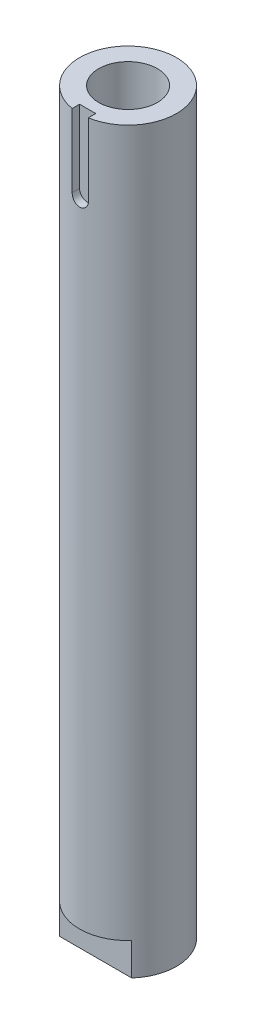
SolidWorks part; units mm, degrees
ref_plane "Front Plane" through (0, 0, 0) normal (0, 0, 1) x (1, 0, 0)
ref_plane "Top Plane" through (0, 0, 0) normal (0, 1, 0) x (1, 0, 0)
ref_plane "Right Plane" through (0, 0, 0) normal (1, 0, 0) x (0, 0, -1)
sketch "Sketch1" plane through (0, 0, 0) normal (0, 1, 0) x (1, 0, 0)
  circle A0 centre (0, 0) radius 9.5
  dimension "D1" = 19
extrude "Boss-Extrude1" add sketch "Sketch1" along normal blind 144.78
sketch "Sketch2" plane through (0, 0, 0) normal (0, -1, 0) x (-1, 0, 0)
  line L1 (7.0659, -6.35) -> (-7.0659, -6.35)
  line L3 (7.0659, 6.35) -> (-7.0659, 6.35)
  arc A2 (-7.0659, -6.35) -> (7.0659, -6.35) centre (0, 0) ccw
  arc A3 (7.0659, 6.35) -> (-7.0659, 6.35) centre (0, 0) ccw
  point P0 (0, 0)
  dimension "D1" = 12.7
  dimension "D2" = 6.35
extrude "Cut-Extrude1" cut sketch "Sketch2" against normal blind 6.35
hole_wizard "Tap Drill for 1/4-20 Tap1" positions "Sketch3" profile "Sketch4" hole size "1/4-20" standard "ANSI Inch"
sketch "Sketch3" plane through (0, 0, 0) normal (0, -1, 0) x (-1, 0, 0)
  point P0 (0, 0)
sketch "Sketch4" plane through (0, 0, 0) normal (1, 0, 0) x (0, 0, -1)
  line L0 (0, 0) -> (0, 33.2838)
  line L1 (0, 33.2838) -> (2.5527, 31.75)
  line L2 (2.5527, 31.75) -> (2.5527, 0)
  line L5 (2.5527, 0) -> (0, 0)
  line L10 (0, 33.2838) -> (-2.5527, 31.75) construction
  line L11 (0, -6.35) -> (0, 107.95) construction
  dimension "Hole Dia." = 5.1054
  dimension "Hole Depth" = 31.75
  dimension "Drill Angle" = 118
hole_wizard "Tap Drill for 1/2-20 Tap1" positions "Sketch6" profile "Sketch5" hole size "1/2-20" standard "ANSI Inch"
sketch "Sketch6" plane through (0, 144.78, 0) normal (0, 1, 0) x (1, 0, 0)
  point P1 (0, 0)
sketch "Sketch5" plane through (0, 144.78, 0) normal (1, 0, 0) x (0, 0, 1)
  line L0 (0, 0) -> (0, 35.2076)
  line L1 (0, 35.2076) -> (5.7544, 31.75)
  line L2 (5.7544, 31.75) -> (5.7544, 0)
  line L5 (5.7544, 0) -> (0, 0)
  line L10 (0, 35.2076) -> (-5.7544, 31.75) construction
  line L11 (0, -6.35) -> (0, 107.95) construction
  dimension "Hole Dia." = 11.5087
  dimension "Hole Depth" = 31.75
  dimension "Drill Angle" = 118
ref_plane "Plane1" through (0, 0, 9.5) normal (0, 0, 1) x (1, 0, 0)
sketch "Sketch7" plane through (0, 0, 9.5) normal (0, 0, 1) x (1, 0, 0)
  line L0 (0, 144.78) -> (0, 128.905) construction
  line L1 (9.5, 144.78) -> (-9.5, 144.78) construction
  line L2 (-1.5875, 130.4925) -> (-1.5875, 144.78)
  line L3 (-1.5875, 144.78) -> (1.5875, 144.78)
  line L4 (5.7544, 144.78) -> (-5.7544, 144.78) construction
  line L5 (1.5875, 144.78) -> (1.5875, 130.4925)
  arc A0 (-1.5875, 130.4925) -> (1.5875, 130.4925) centre (0, 130.4925) ccw
  dimension "D2" = 3.175
  dimension "D1" = 15.875
extrude "Cut-Extrude2" cut sketch "Sketch7" against normal blind 1.5875
